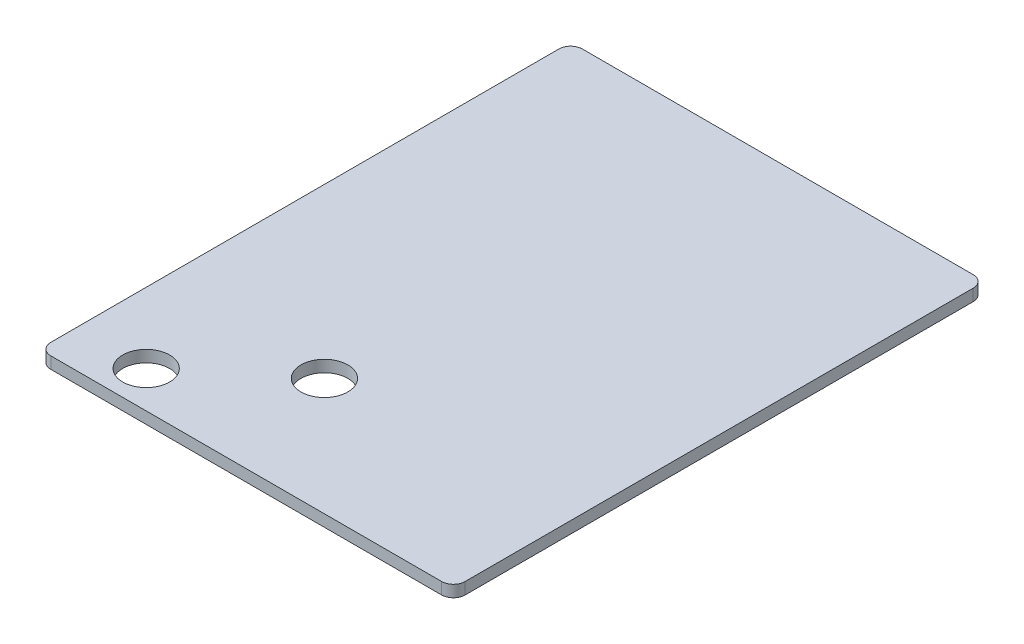
SolidWorks part; units mm, degrees
ref_plane "Plan de face" through (0, 0, 0) normal (0, 0, 1) x (1, 0, 0)
ref_plane "Plan de dessus" through (0, 0, 0) normal (0, 1, 0) x (1, 0, 0)
ref_plane "Plan de droite" through (0, 0, 0) normal (1, 0, 0) x (0, 0, -1)
sketch "Esquisse1" plane through (0, 0, 0) normal (0, 1, 0) x (1, 0, 0)
  line L1 (-53, -68) -> (53, -68)
  line L2 (-53, -68) -> (-53, 68)
  line L3 (-53, 68) -> (53, 68)
  line L4 (53, -68) -> (53, 68)
  line L5 (-53, -68) -> (53, 68) construction
  line L6 (-53, 68) -> (53, -68) construction
  point P0 (0, 0)
  dimension "D1" = 106
  dimension "D2" = 136
extrude "Boss.-Extru.1" add sketch "Esquisse1" along normal blind 3
fillet "Congé1" radius 3 4 edges at (53, 1.5, 68) (53, 1.5, -68) (-53, 1.5, -68) (-53, 1.5, 68)
sketch "Esquisse2" plane through (0, 3, 0) normal (0, 1, 0) x (1, 0, 0)
  line L0 (-50, -68) -> (50, -68) construction
  line L1 (-53, 65) -> (-53, -65) construction
  circle A0 centre (-35, -58.6) radius 6
  circle A1 centre (-10, -38) radius 6
  dimension "D1" = 9.4
  dimension "D2" = 18
  dimension "D3" = 30
  dimension "D4" = 43
extrude "Enlèv. mat.-Extru.1" cut sketch "Esquisse2" against normal blind 10
